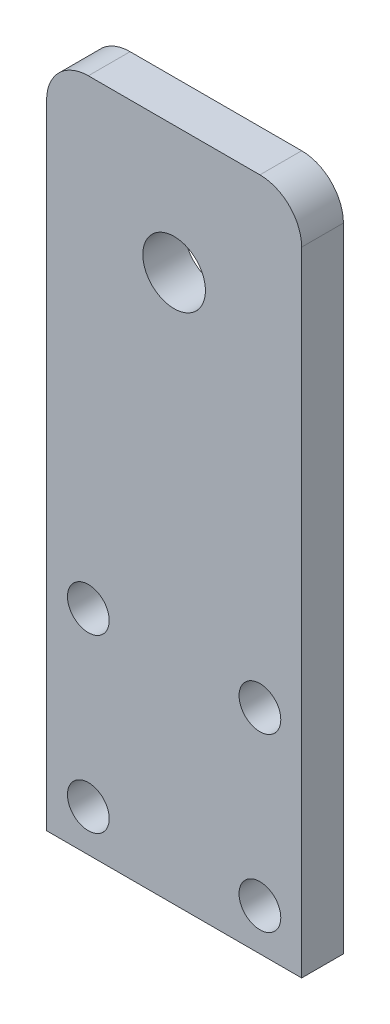
SolidWorks part; units mm, degrees
ref_plane "Front Plane" through (0, 0, 0) normal (0, 0, 1) x (1, 0, 0)
ref_plane "Top Plane" through (0, 0, 0) normal (0, 1, 0) x (1, 0, 0)
ref_plane "Right Plane" through (0, 0, 0) normal (1, 0, 0) x (0, 0, -1)
sketch "Sketch1" plane through (0, 0, 0) normal (0, 0, 1) x (1, 0, 0)
  line L0 (-19.4005, 19.4005) -> (-19.4005, 44.4391)
  line L1 (19.4005, 83.2401) -> (-19.4005, 83.2401)
  line L2 (19.4005, 83.2401) -> (19.4005, 44.4391)
  line L3 (19.4005, 44.4391) -> (-19.4005, 44.4391) construction
  line L4 (-19.4005, 83.2401) -> (-19.4005, 44.4391)
  line L5 (19.4005, 83.2401) -> (-19.4005, 44.4391) construction
  line L6 (19.4005, 44.4391) -> (-19.4005, 83.2401) construction
  line L7 (19.4005, 44.4391) -> (19.4005, 19.4005)
  circle A0 centre (0, 63.8396) radius 4.7625
  point P0 (0, 63.8396)
  line B0 (-19.4005, 19.4005) -> (19.4005, -19.4005) construction
  line B1 (-19.4005, -19.4005) -> (19.4005, 19.4005) construction
  line B2 (-19.4005, -19.4005) -> (19.4005, -19.4005)
  line B3 (19.4005, -19.4005) -> (19.4005, 19.4005)
  line B4 (19.4005, 19.4005) -> (-19.4005, 19.4005)
  line B5 (-19.4005, 19.4005) -> (-19.4005, -19.4005)
  circle B6 centre (13.0505, 13.0505) radius 3.175
  arc B7 (1.434, 68.3811) -> (-1.5379, 59.3322) centre (0, 63.8396) ccw
  circle B8 centre (-13.0505, 13.0505) radius 3.175
  circle B9 centre (-13.0505, -13.0505) radius 3.175
  circle B10 centre (13.0505, -13.0505) radius 3.175
  spline B11 degree 3 poles (-1.5379, 59.3322) (-1.5363, 59.3675) (-1.5114, 59.3979) (-1.4517, 59.4354) (-1.4179, 59.4466) (-1.3166, 59.4735) (-1.2475, 59.4817) (-1.0395, 59.5022) (-0.8998, 59.5079) (-0.4818, 59.5318) (-0.2035, 59.5535) (0.6252, 59.6833) (1.1495, 59.8561) (2.1327, 60.3909) (2.5633, 60.7368) (3.1077, 61.3756) (3.2661, 61.6022) (3.5375, 62.0824) (3.6509, 62.3388) (3.825, 62.8681) (3.8854, 63.1379) (3.9545, 63.6872) (3.9627, 63.9695) (3.9259, 64.5226) (3.8815, 64.7954) (3.7405, 65.3332) (3.6433, 65.5974) (3.2836, 66.3451) (2.9519, 66.8021) (2.3703, 67.4024) (2.1613, 67.5888) (1.8414, 67.8593) (1.7331, 67.9476) (1.5783, 68.0886) (1.5275, 68.1368) (1.4622, 68.2187) (1.442, 68.2475) (1.4164, 68.3129) (1.4144, 68.3518) (1.434, 68.3811) knots 0 0 0 0 0.007812 0.007812 0.015625 0.015625 0.03125 0.03125 0.0625 0.0625 0.125 0.125 0.25 0.25 0.375 0.375 0.4375 0.4375 0.5 0.5 0.5625 0.5625 0.625 0.625 0.6875 0.6875 0.75 0.75 0.875 0.875 0.9375 0.9375 0.96875 0.96875 0.984375 0.984375 0.992188 0.992188 1 1 1 1
sketch_block_instance "Block-ForwardMotorPlate-1"
sketch_block "Block-ForwardMotorPlate" parameters "D2"=6.35, "D1"=6.35
extrude "Boss-Extrude1" add sketch "Sketch1" along normal blind 6.35 contours B4 L7 L2 L1 L4 L0 A0 | B4 B5 B2 B3 B10 B9 B8 B6
fillet "Fillet1" radius 6.35 2 edges at (-19.4005, 83.2401, 3.175) (19.4005, 83.2401, 3.175)
